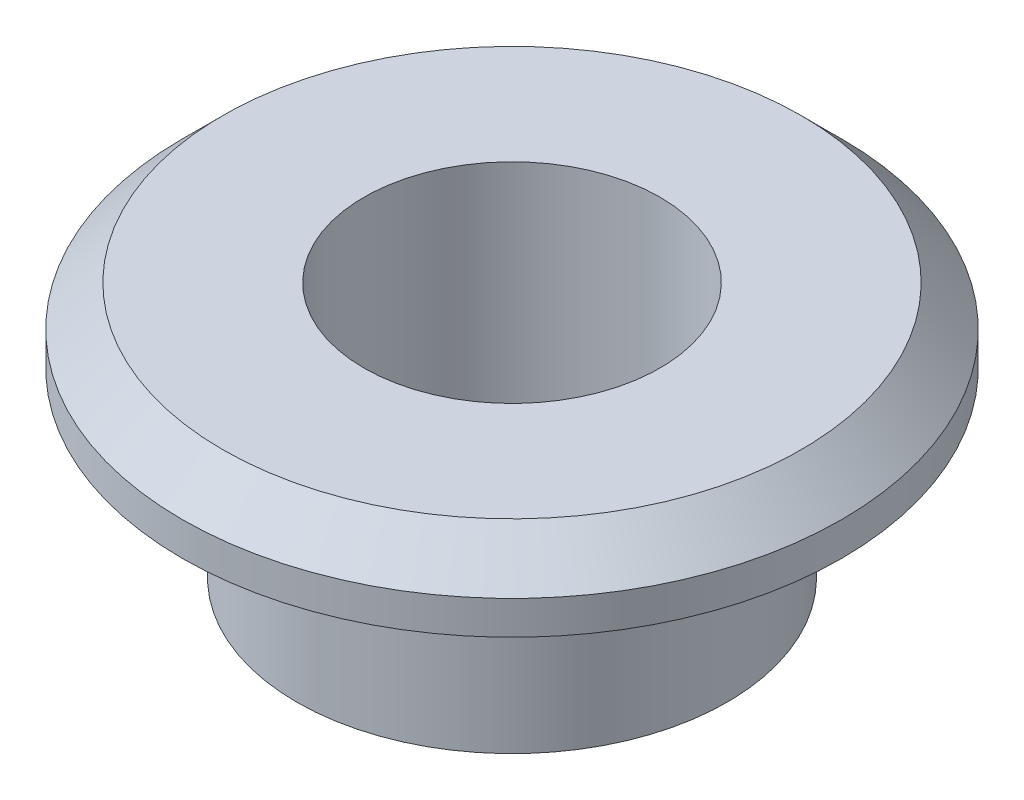
SolidWorks part; units mm, degrees
material "High-leaded brass, UNS C34200"
ref_plane "Front Plane" through (0, 0, 0) normal (0, 0, 1) x (1, 0, 0)
ref_plane "Top Plane" through (0, 0, 0) normal (0, 1, 0) x (1, 0, 0)
ref_plane "Right Plane" through (0, 0, 0) normal (1, 0, 0) x (0, 0, -1)
sketch "Sketch1" plane through (0, 0, 0) normal (0, 0, 1) x (1, 0, 0)
  line L0 (0, 9.7911) -> (0, 0) construction
  line L1 (1.1, 1.9) -> (1.1, 0)
  line L2 (1.1, 0) -> (1.6, 0)
  line L3 (1.6, 0) -> (1.6, 1.35)
  line L4 (1.6, 1.35) -> (2.45, 1.35)
  line L5 (2.45, 1.35) -> (2.45, 1.6)
  line L6 (2.45, 1.6) -> (2.15, 1.9)
  line L7 (2.15, 1.9) -> (1.1, 1.9)
  dimension "D1" = 1.1
  dimension "D2" = 2.45
  dimension "D3" = 1.35
  dimension "D4" = 0.55
  dimension "D5" = 135
  dimension "D6" = 0.3
  dimension "D7" = 1.6
revolve "Revolve1" add sketch "Sketch1" angle 360 about L0
